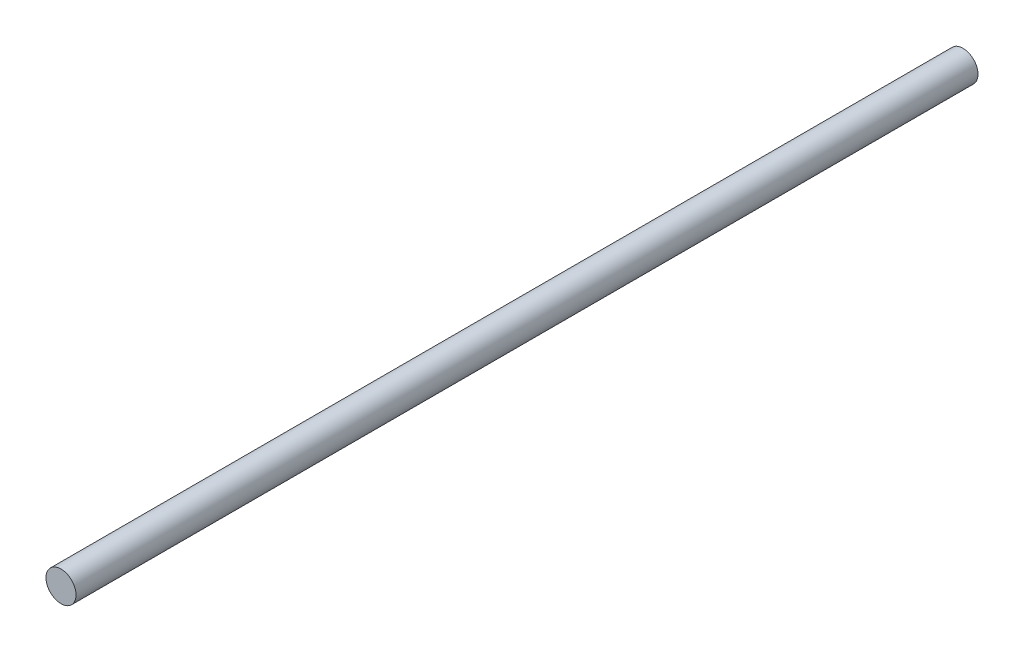
SolidWorks part; units mm, degrees
ref_plane "Front Plane" through (0, 0, 0) normal (0, 0, 1) x (1, 0, 0)
ref_plane "Top Plane" through (0, 0, 0) normal (0, 1, 0) x (1, 0, 0)
ref_plane "Right Plane" through (0, 0, 0) normal (1, 0, 0) x (0, 0, -1)
sketch "Sketch1" plane through (0, 0, 0) normal (0, 0, 1) x (1, 0, 0)
  circle A0 centre (0, 0) radius 0.635
  dimension "D1" = 1.27
extrude "Boss-Extrude1" add sketch "Sketch1" along normal blind 38.1
